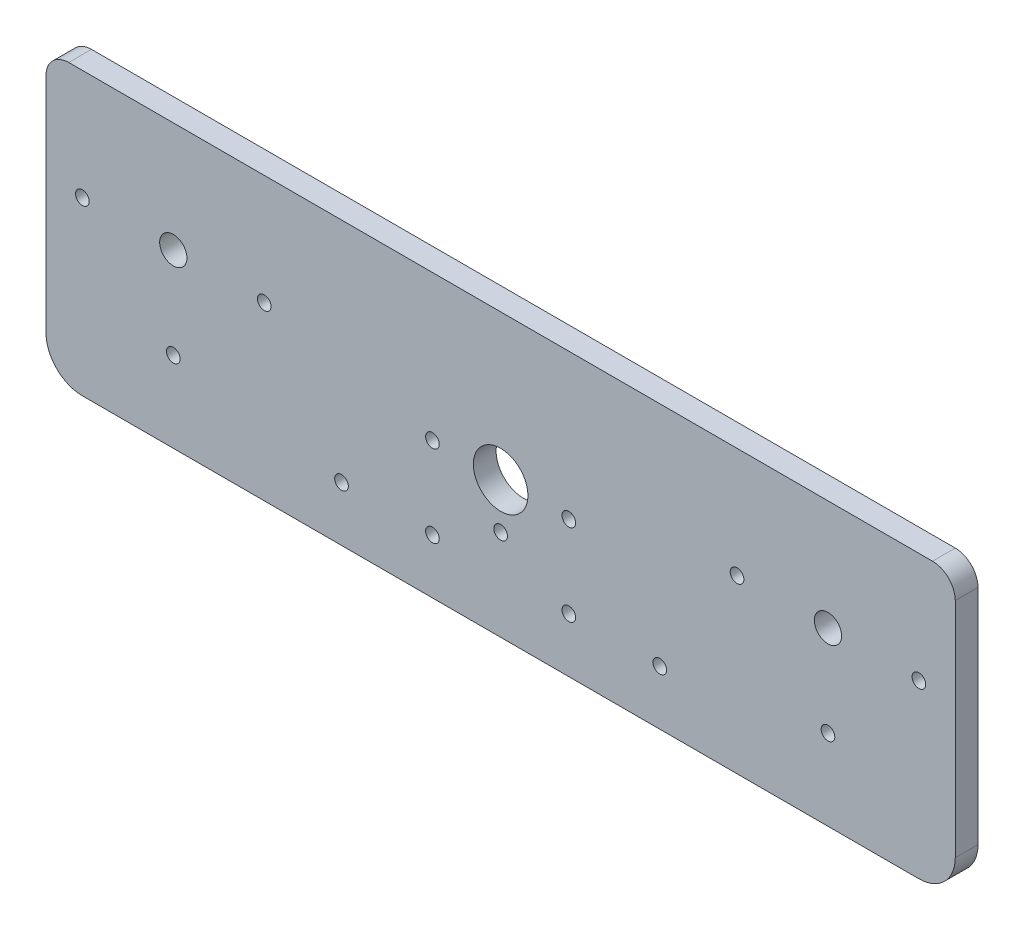
SolidWorks part; units mm, degrees
ref_plane "Alzado" through (0, 0, 0) normal (0, 0, 1) x (1, 0, 0)
ref_plane "Planta" through (0, 0, 0) normal (0, 1, 0) x (1, 0, 0)
ref_plane "Vista lateral" through (0, 0, 0) normal (1, 0, 0) x (0, 0, -1)
sketch "Croquis1" plane through (0, 0, 0) normal (0, 0, 1) x (1, 0, 0)
  line L0 (0, 0) -> (100, 0) construction
  line L1 (0, 0) -> (0, -27) construction
  line L2 (72, 0) -> (72, -19.25) construction
  line L3 (100, 0) -> (100, -49)
  line L4 (92, -57) -> (-92, -57)
  line L5 (0, -57) -> (0, -27) construction
  line L6 (0, 0) -> (0, 5) construction
  line L7 (-100, 5) -> (100, 5)
  line L8 (100, 5) -> (100, 0)
  line L9 (-100, 5) -> (-100, 0)
  line L10 (-100, 0) -> (-100, -49)
  circle A0 centre (0, -27) radius 6
  circle A1 centre (72, -19.25) radius 3
  circle A2 centre (-72, -19.25) radius 3
  circle A3 centre (72, -39.25) radius 1.5
  circle A4 centre (52, -19.25) radius 1.5
  circle A5 centre (92, -19.25) radius 1.5
  circle A6 centre (-72, -19.25) radius 3
  circle A7 centre (-72, -39.25) radius 1.5
  circle A8 centre (-92, -19.25) radius 1.5
  circle A9 centre (-52, -19.25) radius 1.5
  arc A10 (100, -49) -> (92, -57) centre (92, -49) cw
  arc A11 (-100, -49) -> (-92, -57) centre (-92, -49) ccw
  circle A12 centre (15, -45) radius 1.5
  circle A13 centre (35, -45) radius 1.5
  circle A14 centre (-35, -45) radius 1.5
  circle A15 centre (-15, -45) radius 1.5
  circle A16 centre (-15, -27) radius 1.5
  circle A17 centre (15, -27) radius 1.5
  circle A18 centre (0, -37) radius 1.5
  point P34 (100, -57)
  point P37 (-100, -57)
  dimension "D4" = 12
  dimension "D5" = 6
  dimension "D10" = 3
  dimension "D11" = 3
  dimension "D13" = 8
  dimension "D14" = 3
  dimension "D15" = 3
  dimension "D19" = 3
  dimension "D21" = 3
  dimension "D1" = 19.25
  dimension "D2" = 27
  dimension "D3" = 72
  dimension "D6" = 100
  dimension "D7" = 57
  dimension "D8" = 20
  dimension "D9" = 20
  dimension "D12" = 5
  dimension "D16" = 20
  dimension "D17" = 15
  dimension "D18" = 12
  dimension "D20" = 15
  dimension "D22" = 10
extrude "Saliente-Extruir1" add sketch "Croquis1" along normal blind 5 contours L9 L10 L4 L3 L8 L7 A7 A2 A1 A0 A3 A4 A5 A8 A9
fillet "Redondeo1" radius 5 2 edges at (100, 5, 2.5) (-100, 5, 2.5)
